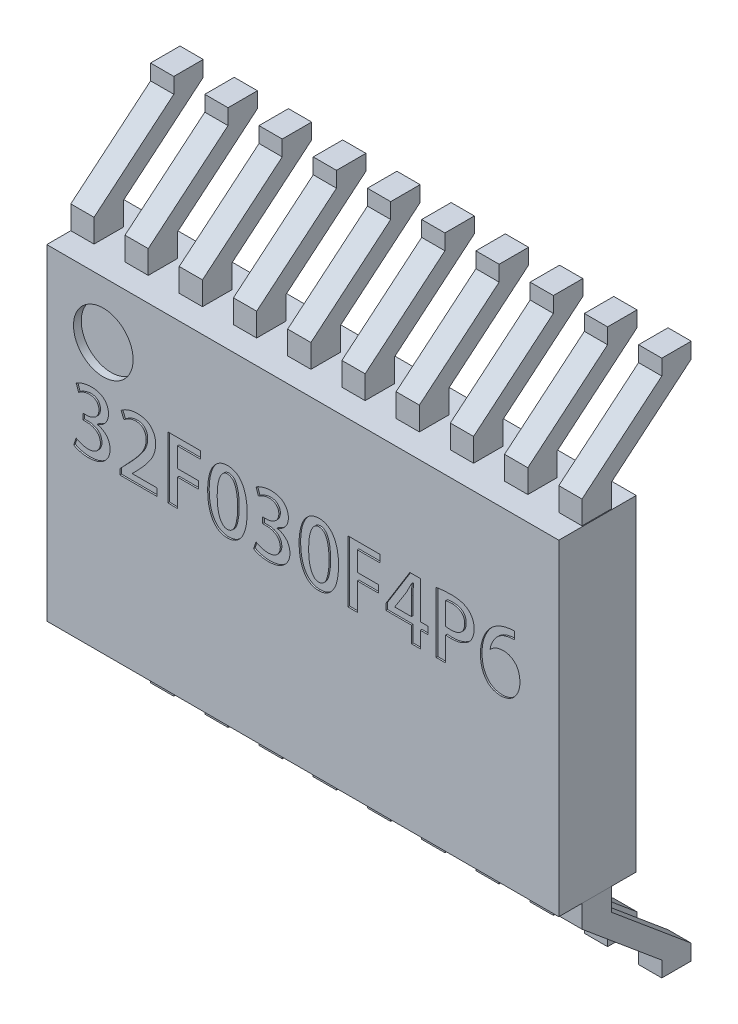
SolidWorks part; units mm, degrees
ref_plane "Plan de face" through (0, 0, 0) normal (0, 0, 1) x (1, 0, 0)
ref_plane "Plan de dessus" through (0, 0, 0) normal (0, 1, 0) x (1, 0, 0)
ref_plane "Plan de droite" through (0, 0, 0) normal (1, 0, 0) x (0, 0, -1)
sketch "Esquisse1" plane through (0, 0, 0) normal (0, 0, 1) x (1, 0, 0)
  line L0 (-6.4232, 0) -> (8.5456, 0) construction
  line L1 (0, -6.4764) -> (0, 6.8796) construction
  line L3 (-3.305, 2.105) -> (3.305, 2.105)
  line L4 (-3.305, 2.105) -> (-3.305, -2.105)
  line L5 (-3.305, -2.105) -> (3.305, -2.105)
  line L6 (3.305, 2.105) -> (3.305, -2.105)
  dimension "D1" = 6.61
  dimension "D2" = 4.21
extrude "Corps" add sketch "Esquisse1" along normal blind 1
sketch "Esquisse2" plane through (0, 0, 1) normal (0, 0, 1) x (1, 0, 0)
  line L0 (3.305, 2.105) -> (-3.305, 2.105) construction
  line L2 (-3.305, 2.105) -> (-3.305, -2.105) construction
  circle A0 centre (-2.575, 1.375) radius 0.385
  dimension "D3" = 0.77
  dimension "D1" = 0.73
  dimension "D2" = 0.73
extrude "Enlèv. mat.-Extru.1" cut sketch "Esquisse2" against normal blind 0.1
sketch "Esquisse3" plane through (0, 0, 1) normal (0, 0, 1) x (1, 0, 0)
  text T0 "32F030F4P6" font "@Adobe Heiti Std R" height 0.8
extrude "Texte" cut sketch "Esquisse3" against normal blind 0.02
ref_plane "Plan1" through (0, -1.605, 0) normal (0, -1, 0) x (-1, 0, 0)
ref_plane "Plan2" through (-3.305, 0, 0) normal (-1, 0, 0) x (0, 0, 1)
sketch "Esquisse6" plane through (-3.305, 0, 0) normal (-1, 0, 0) x (0, 0, 1)
  line L10 (0.31, -2.405) -> (0.31, -2.105)
  line L11 (1, -2.105) -> (0, -2.105) construction
  line L12 (0.69, -2.405) -> (0.69, -2.105)
  line L13 (0.31, -2.105) -> (0.69, -2.105)
  line L14 (0, 2.105) -> (0, -2.105) construction
  line L15 (0.31, -2.405) -> (-0.7199, -3.265)
  line L16 (-0.7199, -3.265) -> (-0.7199, -3.465)
  line L17 (-0.7199, -3.465) -> (-0.34, -3.465)
  line L18 (-0.34, -3.465) -> (-0.34, -3.265)
  line L19 (-0.34, -3.265) -> (0.69, -2.405)
  point P22 (-0.34, -3.365)
  dimension "D10" = 0.3
  dimension "D11" = 0.31
  dimension "D12" = 0.38
  dimension "D13" = 0.3799
  dimension "D14" = 1.03
  dimension "D15" = 0.2
  dimension "D16" = 0.2
  dimension "D17" = 0.86
extrude "Boss.-Extru.3" add sketch "Esquisse6" against normal blind 0.3
pattern_linear "Répétition linéaire2" count 10 spacing 0.7 along (1, 0, 0) of "Boss.-Extru.3"
mirror "Symétrie1" about plane through (0, 0, 0) normal (0, 1, 0) of "Répétition linéaire2", "Boss.-Extru.3"
